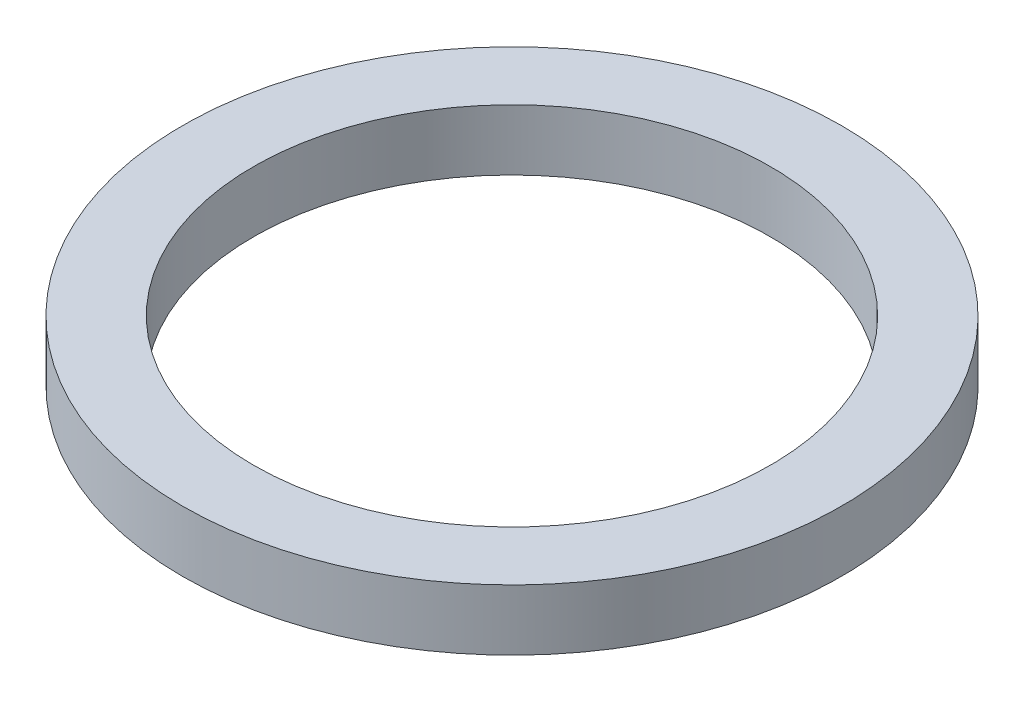
SolidWorks part; units mm, degrees
material "1023 Chapa de acero al carbono (SS)"
ref_plane "Alzado" through (0, 0, 0) normal (0, 0, 1) x (1, 0, 0)
ref_plane "Planta" through (0, 0, 0) normal (0, 1, 0) x (1, 0, 0)
ref_plane "Vista lateral" through (0, 0, 0) normal (1, 0, 0) x (0, 0, -1)
sketch "Sketch1" plane through (0, 0, 0) normal (0, 1, 0) x (1, 0, 0)
  circle A0 centre (0, 0) radius 32.5
  circle A1 centre (0, 0) radius 25.5
  dimension "D1" = 51
  dimension "D2" = 65
extrude "Extrude1" add sketch "Sketch1" along normal blind 6
